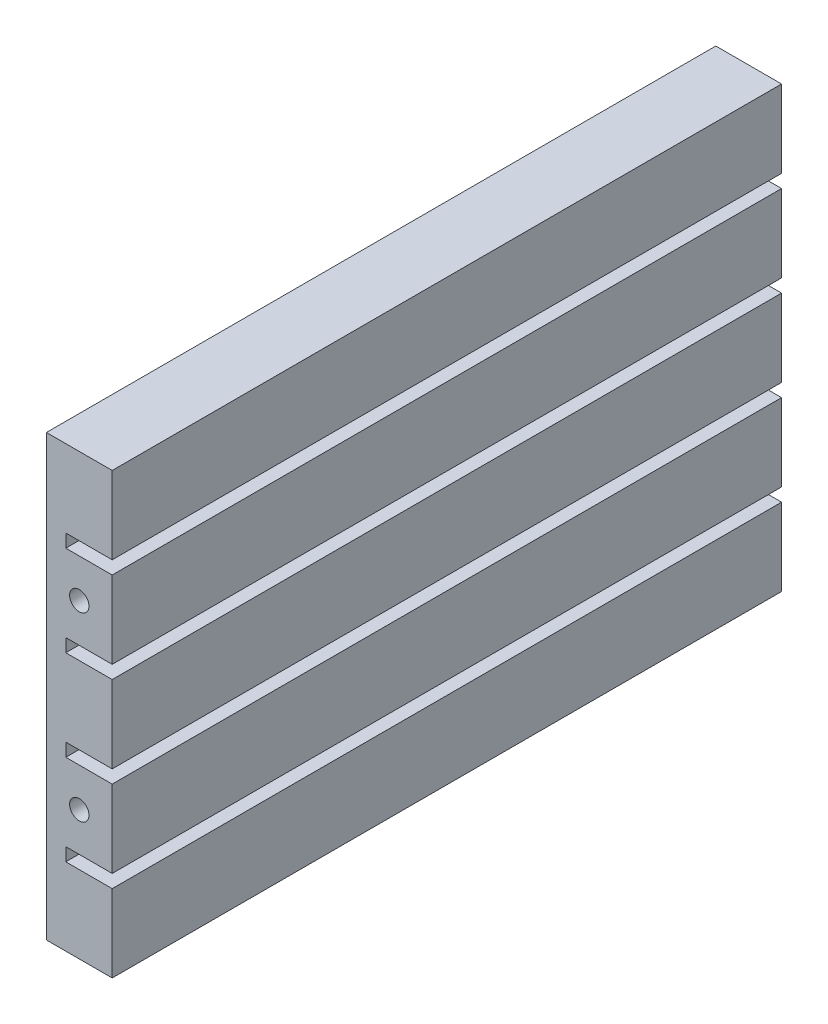
SolidWorks part; units mm, degrees
material "6061-T6 (SS)"
ref_plane "Front Plane" through (0, 0, 0) normal (0, 0, 1) x (1, 0, 0)
ref_plane "Top Plane" through (0, 0, 0) normal (0, 1, 0) x (1, 0, 0)
ref_plane "Right Plane" through (0, 0, 0) normal (1, 0, 0) x (0, 0, -1)
sketch "Sketch1" plane through (0, 0, 0) normal (0, 0, 1) x (1, 0, 0)
  line L0 (0, 0) -> (0, 56.8)
  line L1 (0, 56.8) -> (8.5, 56.8)
  line L2 (8.5, 56.8) -> (8.5, 46.8)
  line L3 (8.5, 46.8) -> (2.5, 46.8)
  line L4 (2.5, 46.8) -> (2.5, 45.1)
  line L5 (2.5, 45.1) -> (8.5, 45.1)
  line L6 (8.5, 45.1) -> (8.5, 35.1)
  line L7 (8.5, 35.1) -> (2.5, 35.1)
  line L8 (2.5, 35.1) -> (2.5, 33.4)
  line L9 (2.5, 33.4) -> (8.5, 33.4)
  line L10 (8.5, 33.4) -> (8.5, 23.4)
  line L11 (8.5, 23.4) -> (2.5, 23.4)
  line L12 (2.5, 23.4) -> (2.5, 21.7)
  line L13 (2.5, 21.7) -> (8.5, 21.7)
  line L14 (8.5, 21.7) -> (8.5, 11.7)
  line L15 (8.5, 11.7) -> (2.5, 11.7)
  line L16 (2.5, 11.7) -> (2.5, 10)
  line L17 (2.5, 10) -> (8.5, 10)
  line L18 (8.5, 10) -> (8.5, 0)
  line L19 (8.5, 0) -> (0, 0)
  dimension "D1" = 56.8
  dimension "D2" = 8.5
  dimension "D3" = 10
  dimension "D4" = 1.7
  dimension "D5" = 6
  dimension "D6" = 10
  dimension "D7" = 1.7
  dimension "D8" = 10
  dimension "D9" = 10
  dimension "D10" = 1.7
  dimension "D11" = 1.7
  dimension "D12" = 2.5
  dimension "D13" = 2.5
  dimension "D14" = 2.5
  dimension "D15" = 8.5
  dimension "D16" = 8.5
  dimension "D17" = 8.5
  dimension "D18" = 8.5
extrude "Boss-Extrude1" add sketch "Sketch1" along normal blind 86.5
sketch "Sketch2" plane through (0, 0, 86.5) normal (0, 0, 1) x (1, 0, 0)
  line L0 (8.5, 35.1) -> (8.5, 45.1) construction
  line L6 (2.5, 35.1) -> (8.5, 35.1) construction
  line L8 (8.5, 11.7) -> (8.5, 21.7) construction
  line L9 (8.5, 21.7) -> (2.5, 21.7) construction
  point P0 (4.25, 16.7)
  point P11 (4.25, 40.1)
  dimension "D1" = 4.25
  dimension "D2" = 5
  dimension "D3" = 4.25
  dimension "D4" = 5
hole_wizard "M3x0.5 Tapped Hole2" positions "Sketch3" profile "Sketch4" tap size "M3x0.5" standard "ANSI Metric"
sketch "Sketch3" plane through (0, 0, 86.5) normal (0, 0, 1) x (1, 0, 0)
  point P0 (4.25, 40.1)
  point P3 (4.25, 16.7)
sketch "Sketch4" plane through (4.25, 40.1, 86.5) normal (1, 0, 0) x (0, -1, 0)
  line L0 (0, 0) -> (0, 5.7511)
  line L1 (0, 5.7511) -> (1.25, 5)
  line L2 (1.25, 5) -> (1.25, 0)
  line L5 (1.25, 0) -> (0, 0)
  line L10 (0, 5.7511) -> (-1.25, 5) construction
  line L11 (0, -6.35) -> (0, 107.95) construction
  dimension "Tap Drill Dia." = 2.5
  dimension "Tap Drill Depth" = 5
  dimension "Drill Angle" = 118
ref_plane "Plane1" through (0, 0, 43.25) normal (0, 0, 1) x (1, 0, 0)
mirror "Mirror1" about plane through (0, 0, 43.25) normal (0, 0, 1) of "M3x0.5 Tapped Hole2"
sketch "Sketch5" plane through (0, 0, 0) normal (-1, 0, 0) x (0, 0, 1)
  line L1 (86.5, 56.8) -> (0, 56.8) construction
  line L5 (0, 56.8) -> (0, 0) construction
  line L7 (86.5, 0) -> (0, 0) construction
  line L8 (86.5, 56.8) -> (86.5, 0) construction
  point P0 (78.25, 5)
  point P3 (8.25, 5)
  point P4 (8.25, 51.8)
  point P7 (78.25, 51.8)
  dimension "D1" = 5
  dimension "D2" = 8.25
  dimension "D3" = 70
  dimension "D4" = 5
  dimension "D5" = 5
  dimension "D6" = 8.25
  dimension "D7" = 8.25
  dimension "D8" = 5
hole_wizard "M3x0.5 Tapped Hole1" positions "Sketch10" profile "Sketch11" tap size "M3x0.5" standard "ANSI Metric"
sketch "Sketch10" plane through (0, 0, 0) normal (-1, 0, 0) x (0, 0, 1)
  line L0 (43.25, 56.8) -> (43.25, 0) construction
  line L1 (86.5, 56.8) -> (0, 56.8) construction
  line L2 (86.5, 0) -> (0, 0) construction
  line L7 (43.25, 51.8) -> (8.25, 51.8) construction
  line L12 (43.25, 5) -> (8.25, 5) construction
  point P16 (8.25, 51.8)
  point P26 (8.25, 5)
sketch "Sketch11" plane through (0, 5, 8.25) normal (0, 1, 0) x (0, 0, 1)
  line L0 (0, 0) -> (0, 5.7511)
  line L1 (0, 5.7511) -> (1.25, 5)
  line L2 (1.25, 5) -> (1.25, 0)
  line L5 (1.25, 0) -> (0, 0)
  line L10 (0, 5.7511) -> (-1.25, 5) construction
  line L11 (0, -6.35) -> (0, 107.95) construction
  dimension "Tap Drill Dia." = 2.5
  dimension "Tap Drill Depth" = 5
  dimension "Drill Angle" = 118
ref_plane "Plane2" through (0, 0, 43.25) normal (0, 0, -1) x (-1, 0, 0)
mirror "Mirror2" about plane through (0, 0, 43.25) normal (0, 0, -1) of "M3x0.5 Tapped Hole1"
